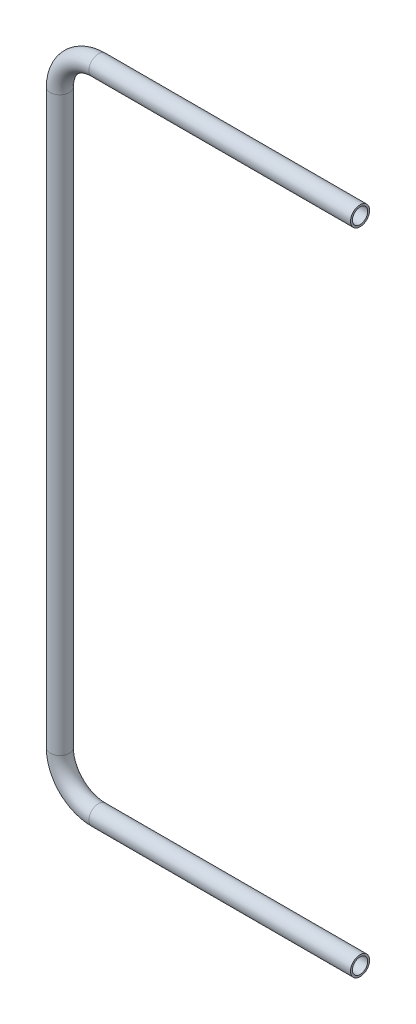
SolidWorks part; units mm, degrees
material "6061-T6 (SS)"
ref_plane "Front Plane" through (0, 0, 0) normal (0, 0, 1) x (1, 0, 0)
ref_plane "Top Plane" through (0, 0, 0) normal (0, 1, 0) x (1, 0, 0)
ref_plane "Right Plane" through (0, 0, 0) normal (1, 0, 0) x (0, 0, -1)
sketch "Sketch1" plane through (0, 0, 0) normal (0, 0, 1) x (1, 0, 0)
  line L0 (0, 0) -> (-457.2, 0)
  line L1 (-524.7005, 67.5005) -> (-524.7005, 1067.562)
  line L2 (-457.2, 1135.0625) -> (0, 1135.0625)
  arc A0 (-457.2, 0) -> (-524.7005, 67.5005) centre (-457.2, 67.5005) cw
  arc A1 (-457.2, 1135.0625) -> (-524.7005, 1067.562) centre (-457.2, 1067.562) ccw
  dimension "D1" = 67.5005
  dimension "D2" = 67.5005
  dimension "D3" = 524.7005
  dimension "D4" = 1135.0625
sketch "Sketch2" plane through (0, 0, 0) normal (1, 0, 0) x (0, 0, -1)
  circle A0 centre (0, 0) radius 16.7005
  circle A1 centre (0, 0) radius 13.335
  dimension "D1" = 33.401
  dimension "D2" = 26.67
sweep "Sweep1" add profiles "Sketch2" path "Sketch1"
